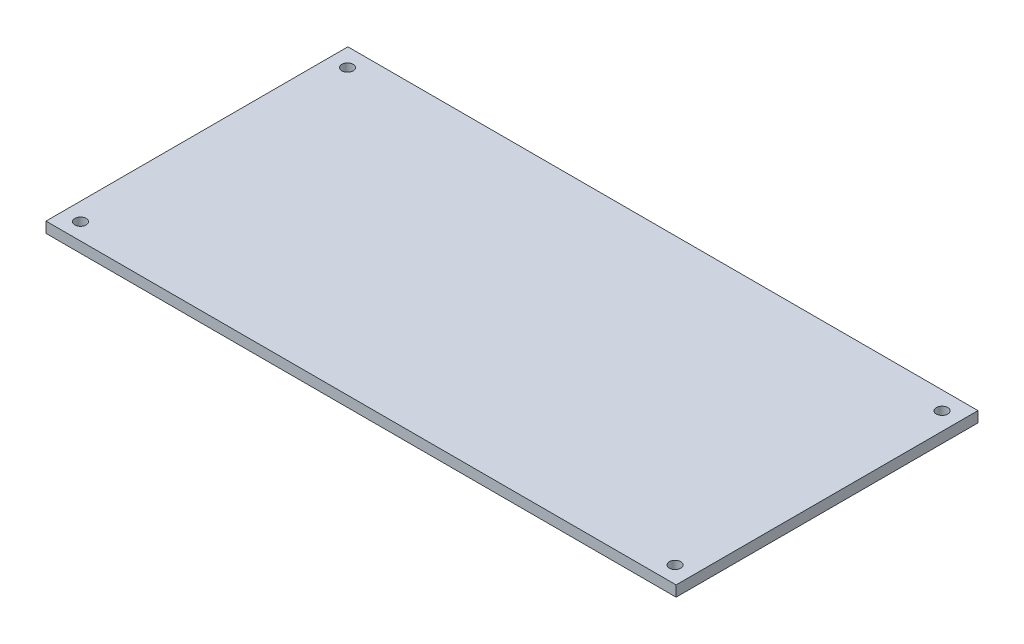
SolidWorks part; units mm, degrees
ref_plane "Front Plane" through (0, 0, 0) normal (0, 0, 1) x (1, 0, 0)
ref_plane "Top Plane" through (0, 0, 0) normal (0, 1, 0) x (1, 0, 0)
ref_plane "Right Plane" through (0, 0, 0) normal (1, 0, 0) x (0, 0, -1)
sketch "Sketch1" plane through (0, 0, 0) normal (0, 1, 0) x (1, 0, 0)
  line L1 (-88.5, -42.4) -> (88.5, -42.4)
  line L2 (-88.5, -42.4) -> (-88.5, 42.4)
  line L3 (-88.5, 42.4) -> (88.5, 42.4)
  line L4 (88.5, -42.4) -> (88.5, 42.4)
  line L5 (-88.5, -42.4) -> (88.5, 42.4) construction
  line L6 (-88.5, 42.4) -> (88.5, -42.4) construction
  point P0 (0, 0)
  dimension "D1" = 177
  dimension "D2" = 84.8
extrude "Boss-Extrude1" add sketch "Sketch1" along normal blind 3
sketch "Sketch2" plane through (0, 3, 0) normal (0, 1, 0) x (1, 0, 0)
  circle A0 centre (83.5, -37.7) radius 2.375 construction
  circle A1 centre (83.5, 37.3) radius 2.375 construction
  circle A2 centre (-83.5, 37.3) radius 2.375 construction
  circle A3 centre (-83.5, -37.7) radius 2.375 construction
  circle A4 centre (83.5, -37.7) radius 2.375 construction
  circle A5 centre (83.5, 37.3) radius 2.375 construction
  circle A6 centre (-83.5, 37.3) radius 2.375 construction
  circle A7 centre (-83.5, -37.7) radius 2.375 construction
  circle A8 centre (83.5, -37.7) radius 1.6
  circle A9 centre (83.5, 37.3) radius 1.6
  circle A10 centre (-83.5, 37.3) radius 1.6
  circle A11 centre (-83.5, -37.7) radius 1.6
  dimension "D1" = 3.2
extrude "Cut-Extrude1" cut sketch "Sketch2" against normal through all
